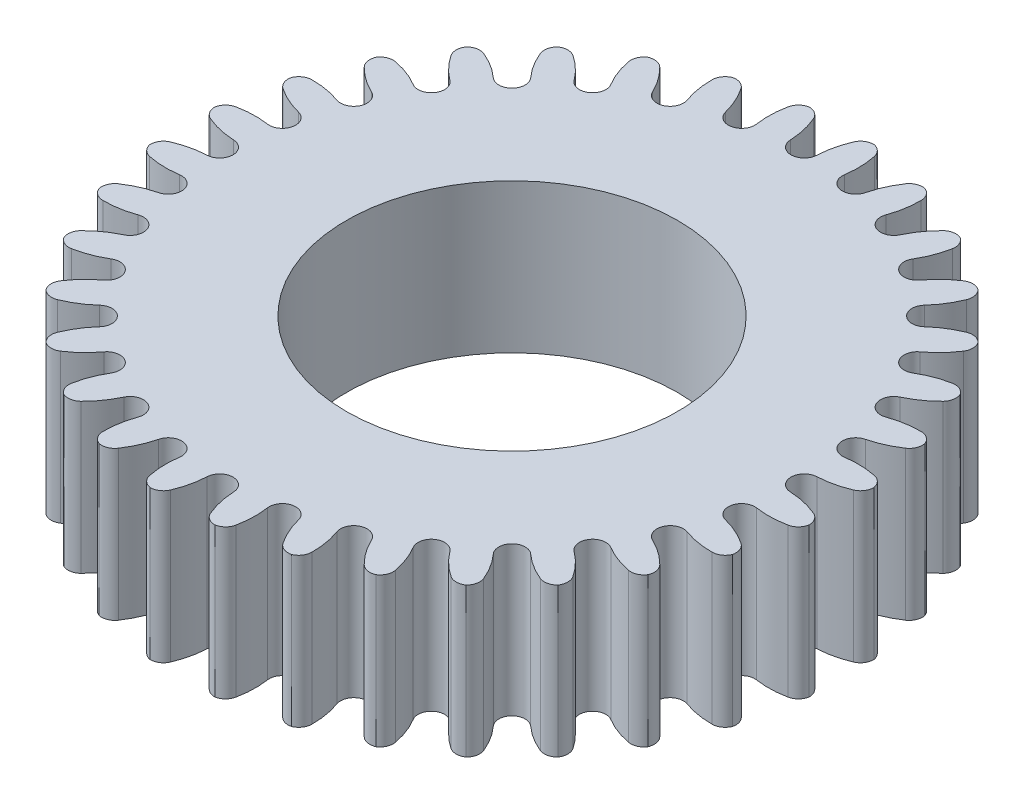
SolidWorks part; units mm, degrees
ref_plane "Front Plane" through (0, 0, 0) normal (0, 0, 1) x (1, 0, 0)
ref_plane "Top Plane" through (0, 0, 0) normal (0, 1, 0) x (1, 0, 0)
ref_plane "Right Plane" through (0, 0, 0) normal (1, 0, 0) x (0, 0, -1)
sketch "Sketch1" plane through (0, 0, 0) normal (0, 1, 0) x (1, 0, 0)
  circle A0 centre (0, 0) radius 20
  dimension "D1" = 40
extrude "Boss-Extrude1" add sketch "Sketch1" along normal blind 9
sketch "Sketch3" plane through (0, 0, 0) normal (0, -1, 0) x (1, 0, 0)
  line L0 (0, -17.6511) -> (0, -60.2569) construction
  arc A0 (0.7992, -17.6144) -> (-0.7992, -17.6144) centre (0, -17.6511) ccw
  arc A1 (0.7992, -17.6144) -> (1.2101, -19.4148) centre (5.9937, -17.3759) ccw
  circle A2 centre (1.946, -19.1011) radius 0.8
  circle A3 centre (0, 0) radius 20 construction
  circle A4 centre (-1.946, -19.1011) radius 0.8
  arc A5 (-0.7992, -17.6144) -> (-1.2101, -19.4148) centre (-5.9937, -17.3759) cw
  dimension "D1" = 1.6
  dimension "D2" = 10.4
  dimension "D3" = 1.45
  dimension "D4" = 1.6
  dimension "D5" = 3.892
extrude "Cut-Extrude1" cut sketch "Sketch3" against normal blind 9
pattern_circular "CirPattern1" count 32 over 360 about axis through (0, 0, 0) along (0, 1, 0) of "Cut-Extrude1"
sketch "Sketch4" plane through (0, 0, 0) normal (0, -1, 0) x (1, 0, 0)
  circle A0 centre (0, 0) radius 10
  dimension "D1" = 20
extrude "Cut-Extrude3" cut sketch "Sketch4" against normal blind 9
